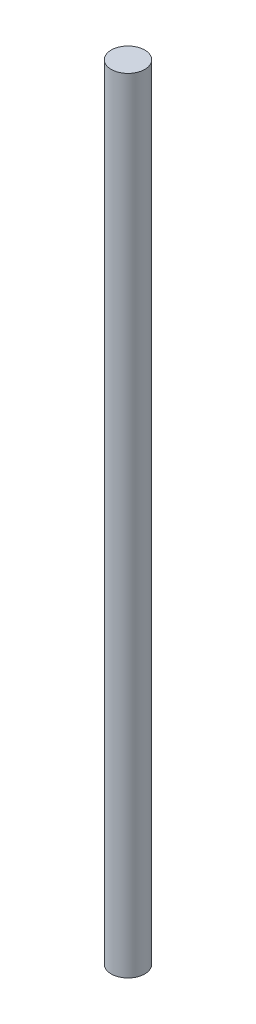
SolidWorks part; units mm, degrees
ref_plane "Front Plane" through (0, 0, 0) normal (0, 0, 1) x (1, 0, 0)
ref_plane "Top Plane" through (0, 0, 0) normal (0, 1, 0) x (1, 0, 0)
ref_plane "Right Plane" through (0, 0, 0) normal (1, 0, 0) x (0, 0, -1)
sketch "Sketch1" plane through (0, 0, 0) normal (0, 1, 0) x (1, 0, 0)
  circle A0 centre (0, 0) radius 1.905
extrude "Boss-Extrude1" add sketch "Sketch1" along normal blind 88.9
equation "\"baseBoxLength\"=3.5"
equation "\"rodDiameter\"=0.15"
equation "\"D1@Boss-Extrude1\"=\"baseBoxLength\""
